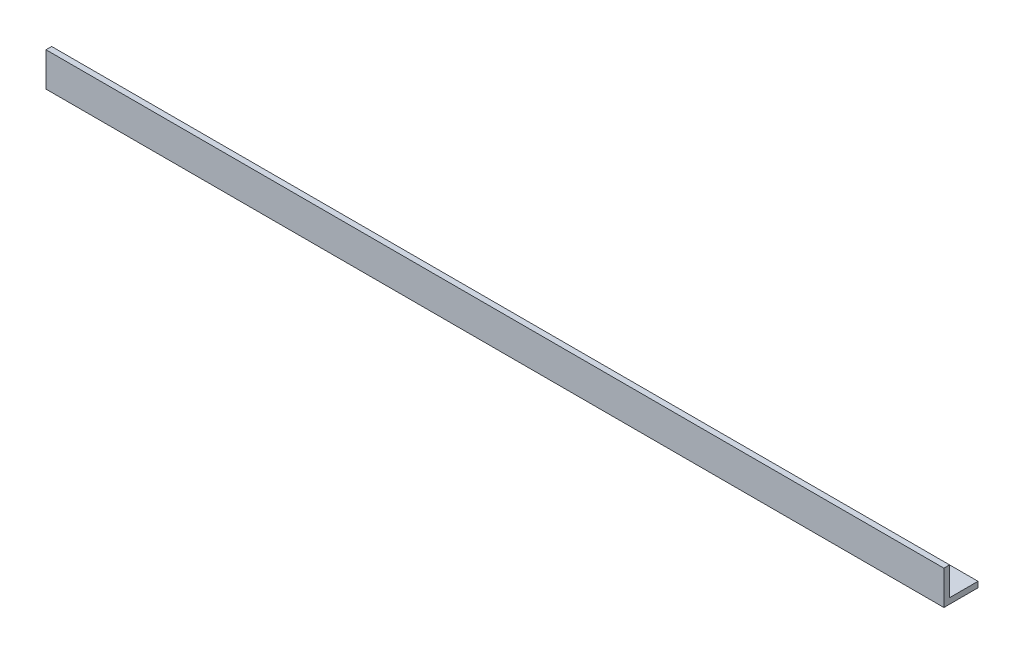
SolidWorks part; units mm, degrees
ref_plane "Front Plane" through (0, 0, 0) normal (0, 0, 1) x (1, 0, 0)
ref_plane "Top Plane" through (0, 0, 0) normal (0, 1, 0) x (1, 0, 0)
ref_plane "Right Plane" through (0, 0, 0) normal (1, 0, 0) x (0, 0, -1)
sketch "Sketch1" plane through (0, 0, 0) normal (1, 0, 0) x (0, 0, -1)
  line L0 (0, 0) -> (0, 1.25)
  line L1 (0, 1.25) -> (-0.25, 1.25)
  line L2 (-0.25, 1.25) -> (-0.25, -0.25)
  line L3 (-0.25, -0.25) -> (0, 0) construction
  line L4 (1.25, -0.25) -> (-0.25, -0.25)
  line L5 (1.25, 0) -> (1.25, -0.25)
  line L6 (0, 0) -> (1.25, 0)
  point P5 (0, -0.028)
  dimension "D1" = 1.5
  dimension "D2" = 45
  dimension "D3" = 0.25
extrude "Boss-Extrude1" add sketch "Sketch1" along normal blind 39.5
